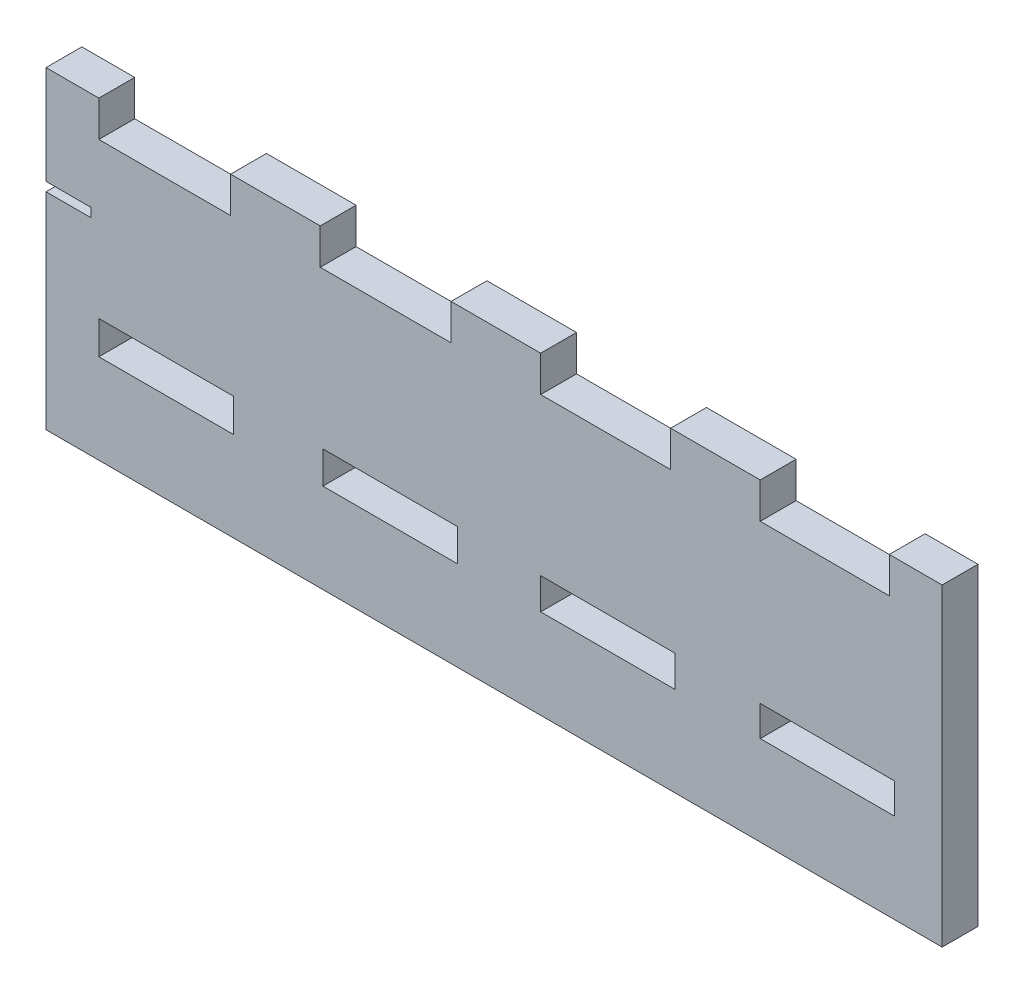
SolidWorks part; units mm, degrees
ref_plane "Ebene vorne" through (0, 0, 0) normal (0, 0, 1) x (1, 0, 0)
ref_plane "Ebene oben" through (0, 0, 0) normal (0, 1, 0) x (1, 0, 0)
ref_plane "Ebene rechts" through (0, 0, 0) normal (1, 0, 0) x (0, 0, -1)
sketch "Skizze1" plane through (0, 0, 0) normal (0, 0, 1) x (1, 0, 0)
  line L0 (5.9, 35) -> (5.9, 31)
  line L1 (0, 0) -> (100, 0)
  line L2 (0, 0) -> (0, 23)
  line L3 (0, 35) -> (5.9, 35)
  line L4 (100, 0) -> (100, 35)
  line L5 (5.9, 31) -> (20.6, 31)
  line L6 (20.6, 31) -> (20.6, 35)
  line L7 (20.6, 35) -> (30.6, 35)
  line L8 (30.6, 35) -> (30.6, 31)
  line L9 (30.6, 31) -> (45.2, 31)
  line L10 (45.2, 31) -> (45.2, 35)
  line L11 (55.2, 35) -> (55.2, 31)
  line L12 (55.2, 31) -> (69.7, 31)
  line L13 (69.7, 31) -> (69.7, 35)
  line L14 (79.7, 35) -> (79.7, 31)
  line L15 (79.7, 31) -> (94.1, 31)
  line L16 (94.1, 31) -> (94.1, 35)
  line L17 (45.2, 35) -> (55.2, 35)
  line L18 (69.7, 35) -> (79.7, 35)
  line L19 (94.1, 35) -> (100, 35)
  line L20 (0, 24) -> (5, 24)
  line L21 (5.9, 13.7) -> (20.9, 13.7)
  line L22 (5.9, 13.7) -> (5.9, 10)
  line L23 (5.9, 10) -> (20.9, 10)
  line L24 (20.9, 13.7) -> (20.9, 10)
  line L25 (30.9, 13.6) -> (45.9, 13.6)
  line L26 (30.9, 13.6) -> (30.9, 10)
  line L27 (30.9, 10) -> (45.9, 10)
  line L28 (45.9, 13.6) -> (45.9, 10)
  line L29 (55.2, 13.5) -> (70.2, 13.5)
  line L30 (55.2, 13.5) -> (55.2, 10)
  line L31 (55.2, 10) -> (70.2, 10)
  line L32 (70.2, 13.5) -> (70.2, 10)
  line L33 (79.7, 13.4) -> (94.7, 13.4)
  line L34 (79.7, 13.4) -> (79.7, 10)
  line L35 (79.7, 10) -> (94.7, 10)
  line L36 (94.7, 13.4) -> (94.7, 10)
  line L37 (5, 24) -> (5, 23)
  line L38 (5, 23) -> (0, 23)
  line L39 (0, 24) -> (0, 35)
  dimension "D1" = 4
  dimension "D2" = 14.7
  dimension "D3" = 14.6
  dimension "D4" = 14.5
  dimension "D5" = 14.4
  dimension "D6" = 35
  dimension "D7" = 100
  dimension "D8" = 10
  dimension "D9" = 3.7
  dimension "D10" = 15
  dimension "D11" = 3.6
  dimension "D12" = 15
  dimension "D13" = 15
  dimension "D14" = 15
  dimension "D15" = 3.5
  dimension "D16" = 3.4
  dimension "D17" = 10
  dimension "D18" = 10
  dimension "D19" = 1
  dimension "D20" = 5
  dimension "D21" = 11
extrude "Aufsatz-Linear austragen1" add sketch "Skizze1" along normal blind 4
